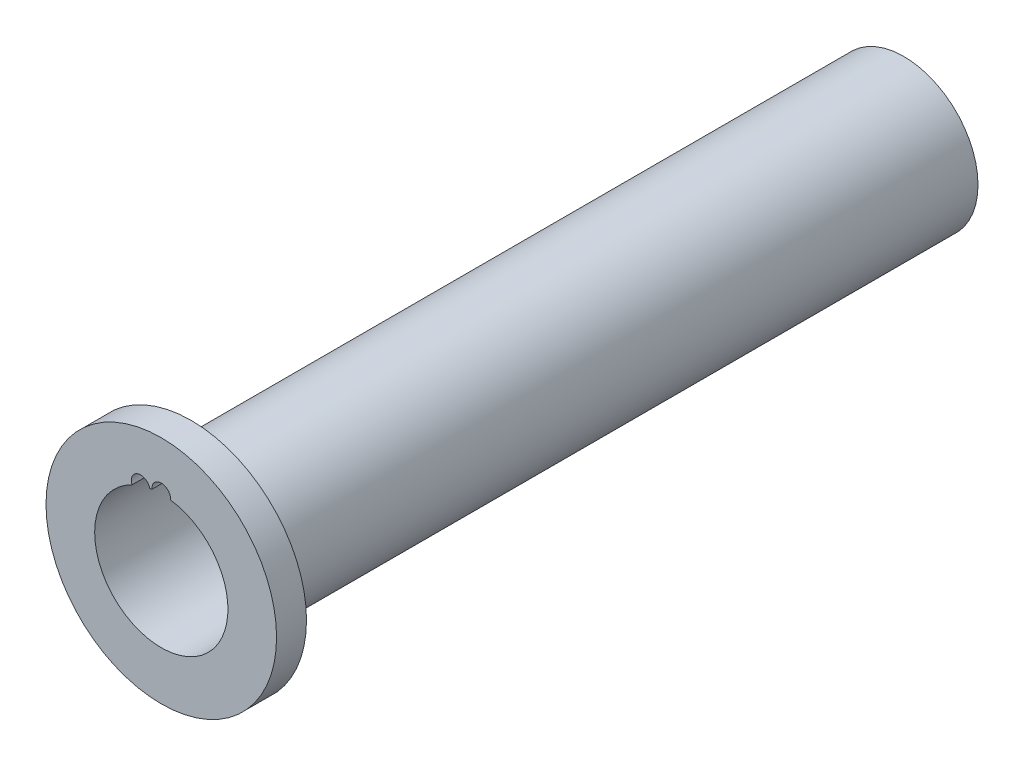
SolidWorks part; units mm, degrees
material "ABS PC"
ref_plane "Front Plane" through (0, 0, 0) normal (0, 0, 1) x (1, 0, 0)
ref_plane "Top Plane" through (0, 0, 0) normal (0, 1, 0) x (1, 0, 0)
ref_plane "Right Plane" through (0, 0, 0) normal (1, 0, 0) x (0, 0, -1)
sketch "Sketch1" plane through (0, 0, 0) normal (0, 0, 1) x (1, 0, 0)
  circle A0 centre (0, 0) radius 4.45
  circle A2 centre (0, 0) radius 4.95
  dimension "D1" = 8.9
  dimension "D2" = 0.5
extrude "Boss-Extrude1" add sketch "Sketch1" along normal blind 47.6
sketch "Sketch5" plane through (0, 0, 47.6) normal (0, 0, 1) x (1, 0, 0)
  circle A0 centre (0, 0) radius 4.45
  circle A1 centre (0, 0) radius 7.7
  dimension "D1" = 15.4
extrude "Boss-Extrude3" add sketch "Sketch5" along normal blind 2
sketch "Sketch2" plane through (0, 0, 47.6) normal (0, 0, -1) x (-1, 0, 0)
  line L0 (0, 0) -> (0, 4.95) construction
  line L1 (0, 0) -> (1.5296, 4.7077) construction
  line L2 (1.5296, 4.7077) -> (1.3751, 4.2322) construction
  line L3 (0, 4.95) -> (0, 4.45) construction
  circle A1 centre (0, 0) radius 4.45 construction
  circle A6 centre (0, 4.45) radius 0.625
  circle A7 centre (1.3751, 4.2322) radius 0.625
  dimension "D2" = 1.25
  dimension "D3" = 1.25
  dimension "D1" = 18
extrude "Cut-Extrude1" cut sketch "Sketch2" along normal blind 0.7 and the other way up to next
